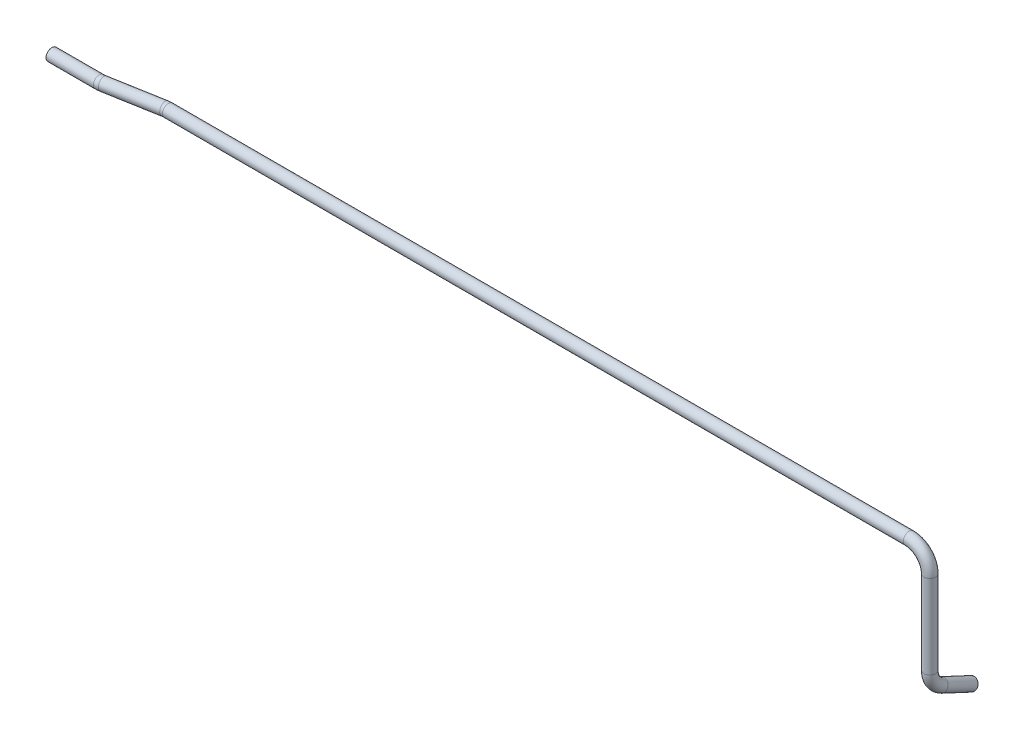
SolidWorks part; units mm, degrees
ref_plane "Plane1" through (0, 0, 0) normal (0, 0, 1) x (1, 0, 0)
ref_plane "Plane2" through (0, 0, 0) normal (0, 1, 0) x (1, 0, 0)
ref_plane "Plane3" through (0, 0, 0) normal (1, 0, 0) x (0, 0, -1)
sketch3d "3DSketch1"
  line L0 (0, 0, 0) -> (48.1627, 0, 0)
  line L1 (50, 0, 0) -> (50, 0, -10) construction
  line L2 (50, 0, -10) -> (106.7128, 0, -10) construction
  line L3 (51.8093, 0, -0.319) -> (104.9035, 0, -9.681)
  line L4 (108.5501, 0, -10) -> (862.4434, 0, -10)
  line L5 (883.4434, -21, -10) -> (883.4434, -106.1215, -10)
  line L6 (883.4434, -125.154, -22.125) -> (883.4434, -139.3631, -52.5965)
  line L7 (883.4434, -139.3631, -52.5965) -> (883.4434, -139.3631, -10) construction
  line L8 (883.4434, -139.3631, -10) -> (883.4434, -119.5, -10) construction
  arc A0 (48.1627, 0, 0) -> (51.8093, 0, -0.319) centre (48.1627, 0, -21) ccw
  arc A1 (108.5501, 0, -10) -> (104.9035, 0, -9.681) centre (108.5501, 0, 11) ccw
  arc A2 (862.4434, 0, -10) -> (883.4434, -21, -10) centre (862.4434, -21, -10) ccw
  arc A3 (883.4434, -106.1215, -10) -> (883.4434, -125.154, -22.125) centre (883.4434, -106.1215, -31) ccw
  point P11 (50, 0, 0)
  point P13 (48.1627, 21, -21)
  point P16 (106.7128, 0, -10)
  point P18 (108.5501, 21, 11)
  point P21 (883.4434, 0, -10)
  point P22 (862.4434, -21, -31)
  point P25 (883.4434, -119.5, -10)
  point P27 (904.4434, -106.1215, -31)
  dimension "D8" = 21
  dimension "D1" = 50
  dimension "D2" = 10
  dimension "D3" = 10
  dimension "D4" = 883.5
  dimension "D5" = 119.5
  dimension "D6" = 115
  dimension "D7" = 47
ref_plane "Plane4" through (0, 0, 0) normal (1, 0, 0) x (0, 0, -1)
sketch "Sketch1" plane through (0, 0, 0) normal (1, 0, 0) x (0, 0, -1)
  circle A0 centre (0, 0) radius 6
  circle A1 centre (0, 0) radius 4.5
  dimension "D1" = 9
  dimension "D2" = 12
sweep "Sweep1" add profiles "Sketch1" path "3DSketch1"
